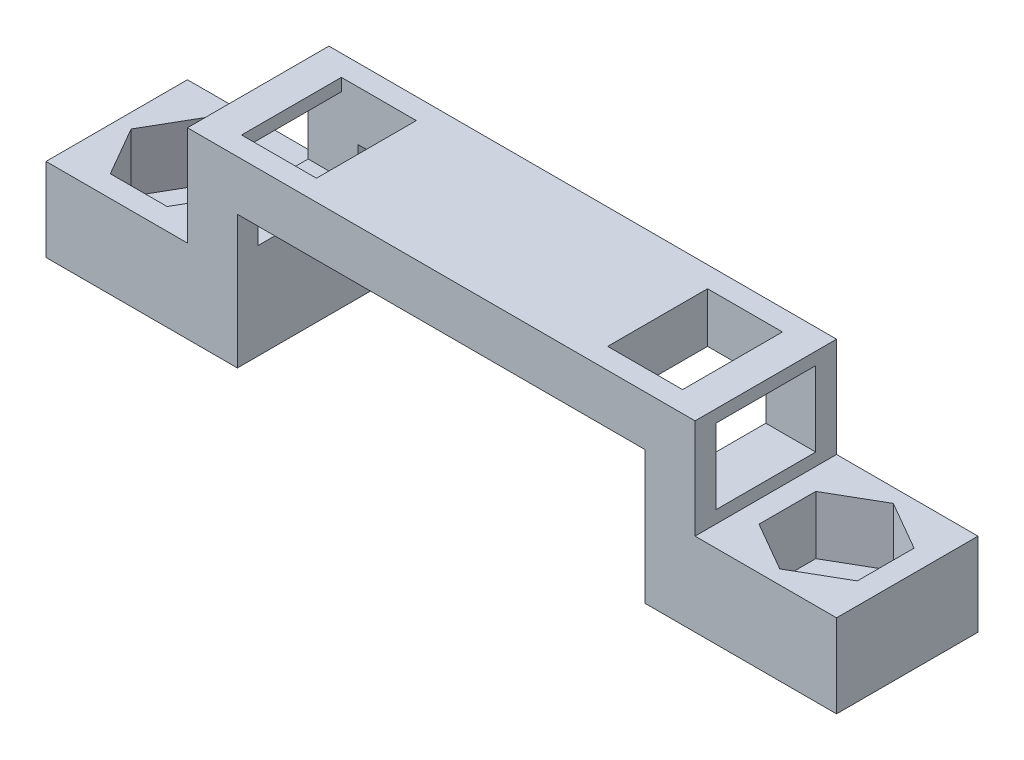
SolidWorks part; units mm, degrees
ref_plane "Front Plane" through (0, 0, 0) normal (0, 0, 1) x (1, 0, 0)
ref_plane "Top Plane" through (0, 0, 0) normal (0, 1, 0) x (1, 0, 0)
ref_plane "Right Plane" through (0, 0, 0) normal (1, 0, 0) x (0, 0, -1)
sketch "Sketch1" plane through (0, 0, 0) normal (0, 1, 0) x (1, 0, 0)
  line L1 (0, 0) -> (8.5, 0)
  line L2 (0, 0) -> (0, 8.5)
  line L3 (0, 8.5) -> (8.5, 8.5)
  line L4 (8.5, 0) -> (8.5, 8.5)
  line L5 (5.9855, 7.196) -> (2.5755, 7.196)
  line L6 (2.5755, 7.196) -> (0.8705, 4.2428)
  line L7 (0.8705, 4.2428) -> (2.5755, 1.2897)
  line L8 (2.5755, 1.2897) -> (5.9855, 1.2897)
  line L9 (5.9855, 1.2897) -> (7.6905, 4.2428)
  line L10 (7.6905, 4.2428) -> (5.9855, 7.196)
  circle A0 centre (4.2805, 4.2428) radius 2.9531 construction
  dimension "D1" = 8.5
  dimension "D2" = 8.5
  dimension "D3" = 3.41
extrude "Boss-Extrude1" add sketch "Sketch1" along normal blind 3.5
sketch "Sketch2" plane through (0, 0, 0) normal (0, -1, 0) x (1, 0, 0)
  line L1 (0, 0) -> (8.5, 0)
  line L2 (0, 0) -> (0, -8.5)
  line L3 (0, -8.5) -> (8.5, -8.5)
  line L4 (8.5, 0) -> (8.5, -8.5)
  circle A0 centre (4.25, -4.25) radius 1.5
  dimension "D1" = 3
extrude "Boss-Extrude2" add sketch "Sketch2" along normal blind 1.5
sketch "Sketch3" plane through (8.5, 0, 0) normal (1, 0, 0) x (0, 0, -1)
  line L1 (0, 3.5) -> (8.5, 3.5)
  line L2 (0, 3.5) -> (0, -1.5)
  line L3 (0, -1.5) -> (8.5, -1.5)
  line L4 (8.5, 3.5) -> (8.5, -1.5)
extrude "Boss-Extrude3" add sketch "Sketch3" along normal blind 3
sketch "Sketch4" plane through (0, 3.5, 0) normal (0, 1, 0) x (1, 0, 0)
  line L0 (0, 0) -> (11.5, 0) construction
  line L1 (11.5, 8.5) -> (8.5, 8.5)
  line L2 (11.5, 8.5) -> (11.5, 0)
  line L3 (11.5, 0) -> (8.5, 0)
  line L4 (8.5, 8.5) -> (8.5, 0)
  dimension "D1" = 3
extrude "Boss-Extrude4" add sketch "Sketch4" along normal blind 6
sketch "Sketch5" plane through (11.5, 0, 0) normal (1, 0, 0) x (0, 0, -1)
  line L0 (8.5, -1.5) -> (8.5, 9.5) construction
  line L1 (0, 9.5) -> (8.5, 9.5)
  line L2 (0, 9.5) -> (0, 6.5)
  line L3 (0, 6.5) -> (8.5, 6.5)
  line L4 (8.5, 9.5) -> (8.5, 6.5)
  dimension "D1" = 3
extrude "Boss-Extrude5" add sketch "Sketch5" along normal blind 27.5
sketch "Sketch6" plane through (0, 6.5, 0) normal (0, -1, 0) x (1, 0, 0)
  line L0 (39, -8.5) -> (11.5, -8.5) construction
  line L1 (39, 0) -> (36, 0)
  line L2 (39, 0) -> (39, -8.5)
  line L3 (39, -8.5) -> (36, -8.5)
  line L4 (36, 0) -> (36, -8.5)
  dimension "D1" = 3
extrude "Boss-Extrude6" add sketch "Sketch6" along normal up to surface (8 mm away) up to face at (5.75, -1.5, -4.25)
sketch "Sketch7" plane through (39, 0, 0) normal (1, 0, 0) x (0, 0, -1)
  line L0 (8.5, -1.5) -> (8.5, 9.5) construction
  line L1 (0, -1.5) -> (8.5, -1.5)
  line L2 (0, -1.5) -> (0, 3.5)
  line L3 (0, 3.5) -> (8.5, 3.5)
  line L4 (8.5, -1.5) -> (8.5, 3.5)
  dimension "D1" = 5
extrude "Boss-Extrude7" add sketch "Sketch7" along normal blind 8.5
sketch "Sketch8" plane through (0, 3.5, 0) normal (0, 1, 0) x (1, 0, 0)
  line L0 (39, 8.5) -> (39, 0) construction
  line L1 (46.2031, 5.955) -> (43.25, 7.66)
  line L2 (43.25, 7.66) -> (40.2969, 5.955)
  line L3 (40.2969, 5.955) -> (40.2969, 2.545)
  line L4 (40.2969, 2.545) -> (43.25, 0.84)
  line L5 (43.25, 0.84) -> (46.2031, 2.545)
  line L6 (46.2031, 2.545) -> (46.2031, 5.955)
  line L11 (47.5, 4.25) -> (39, 4.25) construction
  line L12 (47.5, 8.5) -> (47.5, 0) construction
  line L13 (43.25, 0) -> (43.25, 8.5) construction
  line L14 (47.5, 0) -> (39, 0) construction
  line L15 (47.5, 8.5) -> (39, 8.5) construction
  circle A0 centre (43.25, 4.25) radius 2.9531 construction
  dimension "D1" = 3.41
  dimension "D2" = 0
  dimension "D3" = 0
extrude "Cut-Extrude1" cut sketch "Sketch8" against normal blind 3.5
sketch "Sketch9" plane through (0, 0, 0) normal (0, 1, 0) x (1, 0, 0)
  line L0 (40.2969, 4.25) -> (46.2031, 4.25) construction
  line L1 (40.2969, 5.955) -> (40.2969, 2.545) construction
  line L2 (46.2031, 2.545) -> (46.2031, 5.955) construction
  circle A0 centre (34.75, 4.25) radius 1.5
  dimension "D1" = 3
sketch "Sketch10" plane through (0, 0, 0) normal (0, 1, 0) x (1, 0, 0)
  line L0 (40.2969, 4.25) -> (46.2031, 4.25) construction
  circle A0 centre (43.25, 4.25) radius 1.5
  dimension "3" = 3
extrude "Cut-Extrude3" cut sketch "Sketch10" against normal blind 3.5
sketch "Sketch11" plane through (8.5, 0, 0) normal (-1, 0, 0) x (0, 0, 1)
  line L0 (-4.25, 9.5) -> (-4.25, 3.5) construction
  line L1 (-8.5, 9.5) -> (0, 9.5) construction
  line L2 (-8.5, 3.5) -> (0, 3.5) construction
  line L3 (-8.5, 6.5) -> (0, 6.5) construction
  line L4 (-8.5, 9.5) -> (-8.5, 3.5) construction
  line L5 (0, 9.5) -> (0, 3.5) construction
  line L7 (-7.25, 4.25) -> (-1.25, 4.25)
  line L8 (-7.25, 4.25) -> (-7.25, 8.75)
  line L9 (-7.25, 8.75) -> (-1.25, 8.75)
  line L10 (-1.25, 4.25) -> (-1.25, 8.75)
  line L11 (-7.25, 4.25) -> (-1.25, 8.75) construction
  line L12 (-7.25, 8.75) -> (-1.25, 4.25) construction
  point P12 (-4.25, 6.5)
  dimension "D1" = 6
  dimension "D2" = 4.5
extrude "Cut-Extrude4" cut sketch "Sketch11" against normal blind 3.5
sketch "Sketch12" plane through (0, 9.5, 0) normal (0, 1, 0) x (1, 0, 0)
  line L0 (8.5, 4.25) -> (39, 4.25) construction
  line L1 (8.5, 8.5) -> (8.5, 0) construction
  line L2 (39, 8.5) -> (39, 0) construction
  line L3 (8.5, 8.5) -> (8.5, 0) construction
  line L4 (10.5, 1.25) -> (15, 1.25)
  line L5 (10.5, 1.25) -> (10.5, 7.25)
  line L6 (10.5, 7.25) -> (15, 7.25)
  line L7 (15, 1.25) -> (15, 7.25)
  line L8 (10.5, 1.25) -> (15, 7.25) construction
  line L9 (10.5, 7.25) -> (15, 1.25) construction
  point P6 (12.75, 4.25)
  dimension "D1" = 4.5
  dimension "D2" = 6
  dimension "D3" = 2
extrude "Cut-Extrude5" cut sketch "Sketch12" against normal blind 3.5
sketch "Sketch13" plane through (39, 0, 0) normal (1, 0, 0) x (0, 0, -1)
  line L0 (4.25, 9.5) -> (4.25, 3.5) construction
  line L1 (8.5, 9.5) -> (0, 9.5) construction
  line L2 (8.5, 3.5) -> (0, 3.5) construction
  line L3 (0, 6.5) -> (8.5, 6.5) construction
  line L4 (0, 9.5) -> (0, 3.5) construction
  line L6 (1.25, 4.25) -> (7.25, 4.25)
  line L7 (1.25, 4.25) -> (1.25, 8.75)
  line L8 (1.25, 8.75) -> (7.25, 8.75)
  line L9 (7.25, 4.25) -> (7.25, 8.75)
  line L10 (1.25, 4.25) -> (7.25, 8.75) construction
  line L11 (1.25, 8.75) -> (7.25, 4.25) construction
  point P11 (4.25, 6.5)
  dimension "D1" = 6
  dimension "D2" = 4.5
extrude "Cut-Extrude6" cut sketch "Sketch13" against normal blind 3.5
sketch "Sketch14" plane through (0, 9.5, 0) normal (0, 1, 0) x (1, 0, 0)
  line L0 (8.5, 4.25) -> (39, 4.25) construction
  line L1 (8.5, 8.5) -> (8.5, 0) construction
  line L2 (39, 8.5) -> (39, 0) construction
  line L4 (32.5, 1.25) -> (37, 1.25)
  line L5 (32.5, 1.25) -> (32.5, 7.25)
  line L6 (32.5, 7.25) -> (37, 7.25)
  line L7 (37, 1.25) -> (37, 7.25)
  line L8 (32.5, 1.25) -> (37, 7.25) construction
  line L9 (32.5, 7.25) -> (37, 1.25) construction
  point P6 (34.75, 4.25)
  dimension "D1" = 6
  dimension "D2" = 4.5
  dimension "D3" = 2
extrude "Cut-Extrude7" cut sketch "Sketch14" against normal blind 3.5
